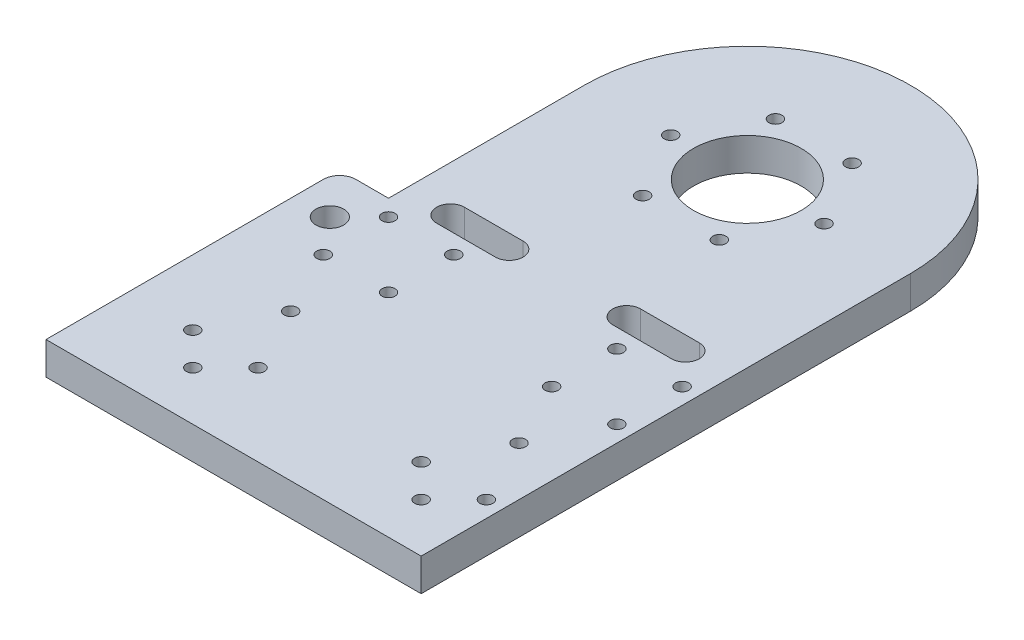
SolidWorks part; units mm, degrees
material "Acrylic (Medium-high impact)"
ref_plane "Front Plane" through (0, 0, 0) normal (0, 0, 1) x (1, 0, 0)
ref_plane "Top Plane" through (0, 0, 0) normal (0, 1, 0) x (1, 0, 0)
ref_plane "Right Plane" through (0, 0, 0) normal (1, 0, 0) x (0, 0, -1)
sketch "Sketch1" plane through (0, 0, 0) normal (0, 1, 0) x (1, 0, 0)
  line L0 (-2.3264, 11.6598) -> (-2.3264, -10.986) construction
  line L1 (-25.8407, 8.1193) -> (-12.3264, 8.1193) construction
  line L2 (-2.3264, 11.6598) -> (-2.3264, -10.986)
  line L3 (-52.3264, -141.8807) -> (47.6736, -141.8807)
  line L4 (47.6736, -141.8807) -> (47.6736, 8.1193)
  line L5 (-2.3264, 8.1193) -> (25.1292, 8.1193) construction
  line L6 (-52.3264, -141.8807) -> (-52.3264, 8.1193)
  arc A0 (47.6736, 8.1193) -> (-52.3264, 8.1193) centre (-2.3264, 8.1193) ccw
  circle A1 centre (-2.3264, 8.1193) radius 16.5
  circle A2 centre (-2.3264, 8.1193) radius 23.5 construction
  circle A3 centre (21.1736, 8.1193) radius 2
  circle A4 centre (9.4236, -12.2323) radius 2
  circle A5 centre (-14.0764, -12.2323) radius 2
  circle A6 centre (-25.8264, 8.1193) radius 2
  circle A7 centre (-14.0764, 28.4709) radius 2
  circle A8 centre (9.4236, 28.4709) radius 2
  circle A9 centre (-47.3264, -116.8807) radius 2
  circle A10 centre (42.6736, -116.8807) radius 2
  circle A11 centre (-37.3264, -126.8807) radius 2
  circle A12 centre (-37.3264, -96.8807) radius 2
  circle A13 centre (-47.3264, -76.8807) radius 2
  circle A14 centre (42.6736, -76.8807) radius 2
  circle A15 centre (-47.3264, -56.8807) radius 2
  circle A16 centre (42.6736, -56.8807) radius 2
  circle A17 centre (-27.3264, -116.8807) radius 2
  circle A18 centre (22.6736, -116.8807) radius 2
  circle A19 centre (-27.3264, -56.8807) radius 2
  circle A20 centre (-27.3264, -76.8807) radius 2
  circle A21 centre (22.6736, -56.8807) radius 2
  circle A22 centre (22.6736, -76.8807) radius 2
  circle A23 centre (32.6736, -96.8807) radius 2
  circle A24 centre (32.6736, -126.8807) radius 2
  point P26 (-2.3264, 8.1193)
  dimension "D1" = 100
  dimension "D3" = 33
  dimension "D4" = 47
  dimension "D5" = 4
  dimension "D7" = 4
  dimension "D8" = 4
  dimension "D9" = 4
  dimension "D10" = 4
  dimension "D11" = 4
  dimension "D12" = 4
  dimension "D13" = 4
  dimension "D14" = 4
  dimension "D20" = 4
  dimension "D21" = 4
  dimension "D22" = 4
  dimension "D23" = 4
  dimension "D24" = 4
  dimension "D25" = 4
  dimension "D28" = 4
  dimension "D54" = 4
  dimension "D2" = 150
  dimension "D6" = 6
  dimension "D15" = 25
  dimension "D16" = 5
  dimension "D17" = 25
  dimension "D18" = 5
  dimension "D19" = 15
  dimension "D26" = 25
  dimension "D27" = 20
  dimension "D29" = 20
  dimension "D30" = 25
  dimension "D31" = 15
  dimension "D32" = 45
  dimension "D33" = 15
  dimension "D34" = 15
  dimension "D35" = 15
  dimension "D36" = 15
  dimension "D37" = 45
  dimension "D38" = 5
  dimension "D39" = 5
  dimension "D40" = 5
  dimension "D41" = 5
  dimension "D42" = 85
  dimension "D43" = 85
  dimension "D44" = 20
  dimension "D45" = 20
  dimension "D46" = 20
  dimension "D47" = 20
  dimension "D48" = 85
  dimension "D49" = 20
  dimension "D50" = 20
  dimension "D51" = 20
  dimension "D52" = 20
  dimension "D53" = 85
extrude "Boss-Extrude3" add sketch "Sketch1" along normal blind 10
sketch "Sketch9" plane through (-52.3264, 0, 0) normal (-1, 0, 0) x (0, 0, 1)
  line L0 (141.8807, 0) -> (-8.1193, 0) construction
  line L1 (141.8807, 10) -> (51.8807, 10)
  line L2 (141.8807, 10) -> (141.8807, 0)
  line L3 (141.8807, 0) -> (51.8807, 0)
  line L4 (51.8807, 10) -> (51.8807, 0)
  dimension "D1" = 90
extrude "Boss-Extrude4" add sketch "Sketch9" along normal blind 15
fillet "Fillet1" radius 5 1 edges at (-67.3264, 5, 51.8807)
sketch "Sketch10" plane through (0, 10, 0) normal (0, 1, 0) x (1, 0, 0)
  line L0 (-52.3264, -51.8807) -> (-52.3264, 8.1193) construction
  line L1 (-62.3264, -51.8807) -> (-52.3264, -51.8807) construction
  circle A0 centre (-56.3264, -65.8807) radius 4.25
  point P4 (0, 0)
  dimension "D1" = 8.5
  dimension "D2" = 4
  dimension "D3" = 14
extrude "Cut-Extrude7" cut sketch "Sketch10" against normal blind 10
sketch "Sketch11" plane through (0, 10, 0) normal (0, 1, 0) x (1, 0, 0)
  line L0 (-67.3264, -141.8807) -> (47.6736, -141.8807) construction
  line L1 (47.6736, -141.8807) -> (47.6736, 8.1193) construction
  line L2 (15.6736, -42.6307) -> (33.6736, -42.6307)
  line L3 (15.6736, -51.1307) -> (33.6736, -51.1307)
  line L4 (-52.3264, -51.8807) -> (-52.3264, 8.1193) construction
  line L5 (-38.3264, -42.6307) -> (-20.3264, -42.6307)
  line L6 (-38.3264, -51.1307) -> (-20.3264, -51.1307)
  arc A0 (15.6736, -42.6307) -> (15.6736, -51.1307) centre (15.6736, -46.8807) ccw
  arc A1 (-20.3264, -51.1307) -> (-20.3264, -42.6307) centre (-20.3264, -46.8807) ccw
  arc A2 (33.6736, -51.1307) -> (33.6736, -42.6307) centre (33.6736, -46.8807) ccw
  arc A3 (-38.3264, -42.6307) -> (-38.3264, -51.1307) centre (-38.3264, -46.8807) ccw
  dimension "D1" = 8.5
  dimension "D2" = 8.5
  dimension "D5" = 8.5
  dimension "D10" = 8.5
  dimension "D3" = 95
  dimension "D4" = 32
  dimension "D6" = 14
  dimension "D7" = 95
  dimension "D8" = 95
  dimension "D9" = 32
  dimension "D11" = 14
  dimension "D12" = 95
extrude "Cut-Extrude8" cut sketch "Sketch11" against normal blind 10 contours A1 L5 A3 L6 | A2 L2 A0 L3
